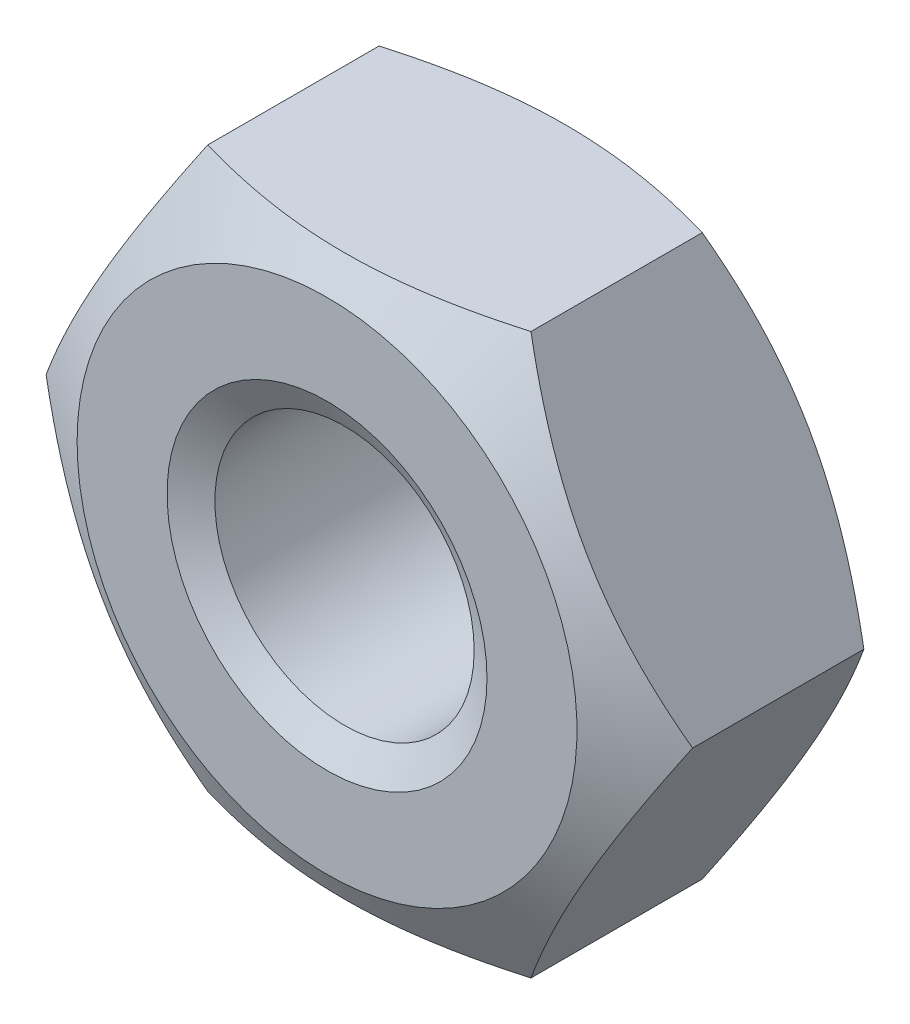
SolidWorks part; units mm, degrees
ref_plane "Front" through (0, 0, 0) normal (0, 0, 1) x (1, 0, 0)
ref_plane "Top" through (0, 0, 0) normal (0, 1, 0) x (1, 0, 0)
ref_plane "Right" through (0, 0, 0) normal (1, 0, 0) x (0, 0, -1)
sketch "Sketch1" plane through (0, 0, 0) normal (0, 0, 1) x (1, 0, 0)
  line L1 (4.0415, 0) -> (2.0207, 3.5)
  line L2 (2.0207, 3.5) -> (-2.0207, 3.5)
  line L3 (-2.0207, 3.5) -> (-4.0415, 0)
  line L4 (-4.0415, 0) -> (-2.0207, -3.5)
  line L5 (-2.0207, -3.5) -> (2.0207, -3.5)
  line L6 (2.0207, -3.5) -> (4.0415, 0)
  circle A0 centre (0, 0) radius 3.5 construction
  circle A1 centre (0, 0) radius 1.621
  dimension "D" = 3.242
  dimension "s" = 7
extrude "BaseNut" add sketch "Sketch1" against normal blind 3.2
cosmetic thread "ThreadCosmetic1" parameters "D"=4
sketch "Sketch2" plane through (0, 0, 0) normal (0, 1, 0) x (1, 0, 0)
  line L0 (-4.0415, 3.2) -> (-3.125, 3.2)
  line L2 (-3.125, 3.2) -> (-4.0415, 2.6709)
  line L3 (-4.0415, 2.6709) -> (-4.0415, 3.2)
  line L4 (0, 3.3759) -> (0, -9.8171) construction
  line L6 (-9.7712, 1.6) -> (9.8853, 1.6) construction
  line L7 (-4.0415, 0.5291) -> (-4.0415, 0)
  line L8 (-3.125, 0) -> (-4.0415, 0.5291)
  line L9 (-4.0415, 0) -> (-3.125, 0)
  dimension "dw" = 6.25
  dimension "D1" = 30
  dimension "D2" = 1.6
revolve "Double-Chamfer" cut sketch "Sketch2" angle 360 about L4
chamfer "EndChamfer" distance 0.379 angle 30 2 edges at (1.621, 0, -3.2) (1.621, 0, 0)
sketch "Sketch3" plane through (0, 0, 0) normal (0, 1, 0) x (1, 0, 0)
  line L0 (-1.9492, 2.821) -> (-1.621, 2.6315)
  line L1 (-1.621, 2.6315) -> (-1.242, 2.6315)
  line L2 (-1.242, 2.6315) -> (-1.242, 3.0105)
  line L3 (-1.242, 3.0105) -> (-1.621, 3.0105)
  line L4 (-1.621, 3.0105) -> (-1.9492, 2.821)
  line L5 (0, 7.4383) -> (0, 16.8806) construction
  dimension "D1" = 0.379
  dimension "D2" = 3.242
revolve "Cut-Revolve10" [suppressed] cut sketch "Sketch3" angle 360 about L5
pattern_linear "LPattern10" [suppressed] count 7 spacing 0.4548 along (0, 0, -1)
equation "\"dw@Sketch2\" = \"s@Sketch1\"-0.75"
equation "\"D2@Sketch2\" = \"m@BaseNut\" / 2"
equation "\"D2@Sketch3\" = \"D@Sketch1\""
equation "\"D1@Sketch3\" =  (\"D@ThreadCosmetic1\"   - \"D@Sketch1\")  / 2"
equation "\"D3@LPattern10\" = \"D1@Sketch3\" * 1.2"
equation "\"D1@LPattern10\" = \"m@BaseNut\"/\"D3@LPattern10\""
